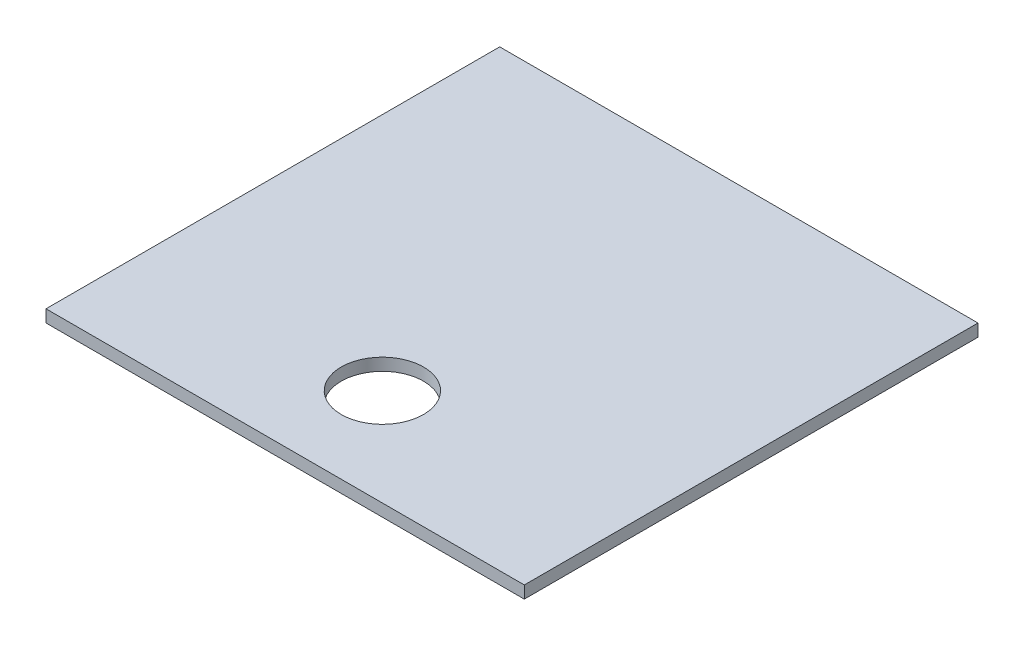
SolidWorks part; units mm, degrees
ref_plane "Alzado" through (0, 0, 0) normal (0, 0, 1) x (1, 0, 0)
ref_plane "Planta" through (0, 0, 0) normal (0, 1, 0) x (1, 0, 0)
ref_plane "Vista lateral" through (0, 0, 0) normal (1, 0, 0) x (0, 0, -1)
sketch "Croquis1" plane through (0, 0, 0) normal (0, 1, 0) x (1, 0, 0)
  line L1 (-36.9, 35) -> (36.9, 35)
  line L2 (-36.9, 35) -> (-36.9, -35)
  line L3 (-36.9, -35) -> (36.9, -35)
  line L4 (36.9, 35) -> (36.9, -35)
  line L5 (-36.9, 35) -> (36.9, -35) construction
  line L6 (-36.9, -35) -> (36.9, 35) construction
  point P0 (0, 0)
  dimension "D1" = 73.8
  dimension "D2" = 70
extrude "Saliente-Extruir1" add sketch "Croquis1" along normal blind 1.9
sketch "Croquis2" plane through (0, 1.9, 0) normal (0, 1, 0) x (1, 0, 0)
  line L0 (36.9, 0) -> (-36.9, 0) construction
  line L1 (36.9, -35) -> (36.9, 35) construction
  line L2 (-36.9, 35) -> (-36.9, -35) construction
  line L3 (-36.9, -35) -> (36.9, -35) construction
  circle A0 centre (0, -20) radius 6.35
  point P8 (0, 0)
  dimension "D1" = 12.7
  dimension "D2" = 15
extrude "Cortar-Extruir1" cut sketch "Croquis2" against normal through all both
